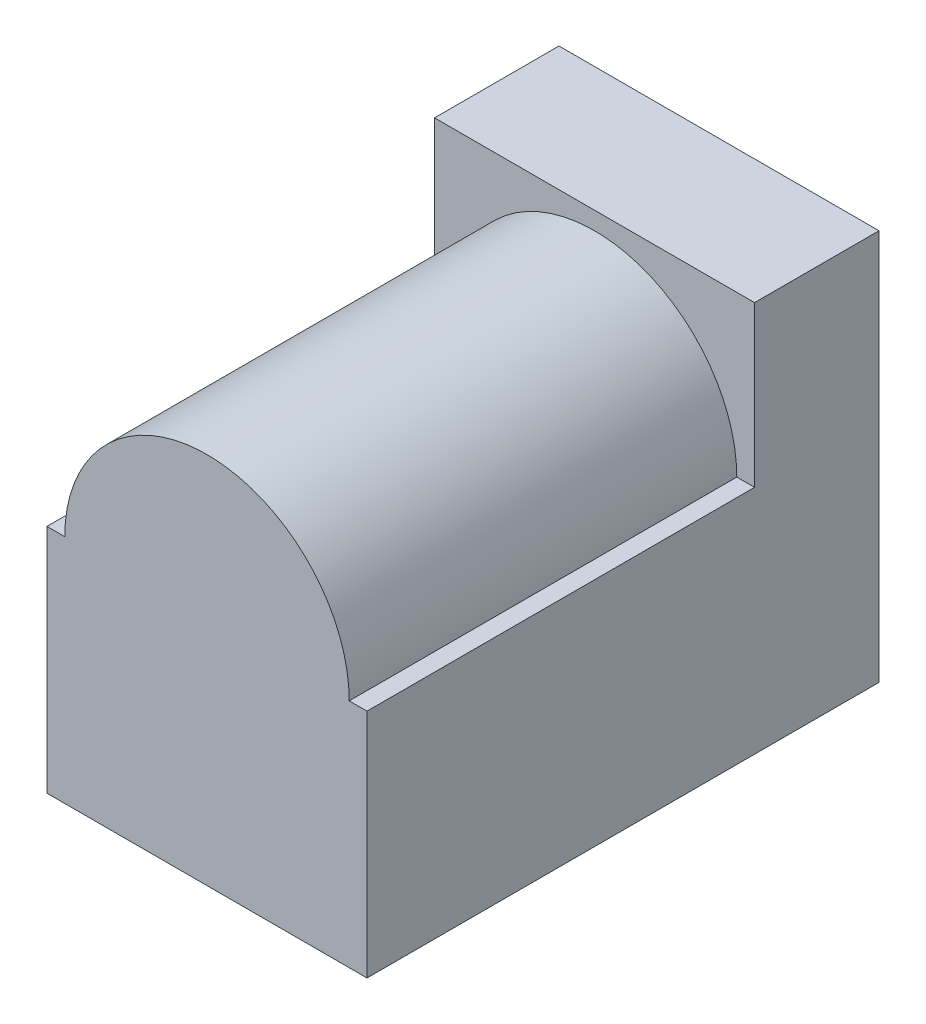
SolidWorks part; units mm, degrees
material "ABS PC"
ref_plane "Front Plane" through (0, 0, 0) normal (0, 0, 1) x (1, 0, 0)
ref_plane "Top Plane" through (0, 0, 0) normal (0, 1, 0) x (1, 0, 0)
ref_plane "Right Plane" through (0, 0, 0) normal (1, 0, 0) x (0, 0, -1)
sketch "Sketch1" plane through (0, 0, 0) normal (0, 0, 1) x (1, 0, 0)
  line L1 (0, 0) -> (9, 0)
  line L2 (0, 0) -> (0, 11)
  line L3 (0, 11) -> (9, 11)
  line L4 (9, 0) -> (9, 11)
  dimension "D1" = 9
  dimension "D2" = 11
extrude "Boss-Extrude1" add sketch "Sketch1" along normal blind 3.5
sketch "Sketch2" plane through (0, 0, 0) normal (0, 0, -1) x (-1, 0, 0)
  line L0 (0, 0) -> (-9, 0) construction
  line L1 (-0.5, 6.5) -> (0, 6.5)
  line L2 (0, 11) -> (0, 0) construction
  line L3 (0, 6.5) -> (0, 0)
  line L4 (0, 0) -> (-9, 0)
  line L5 (-9, 0) -> (-9, 6.5)
  line L6 (-9, 0) -> (-9, 11) construction
  line L7 (-9, 6.5) -> (-8.5, 6.5)
  arc A0 (-0.5, 6.5) -> (-8.5, 6.5) centre (-4.5, 6.5) ccw
  dimension "D1" = 8
  dimension "D2" = 4.5
  dimension "D3" = 6.5
extrude "Boss-Extrude2" add sketch "Sketch2" against normal blind 14.4
sketch "Sketch3" plane through (0, 0, 0) normal (0, 0, -1) x (-1, 0, 0)
  line L0 (0, 0) -> (-9, 0) construction
  line L2 (0, 11) -> (0, 0) construction
  circle A0 centre (-4.5, 6.5) radius 3.25
  circle A1 centre (-4.5, 6.5) radius 1
  dimension "D1" = 6.5
  dimension "D4" = 2
  dimension "D2" = 6.5
  dimension "D3" = 4.5
extrude "Cut-Extrude1" cut sketch "Sketch3" against normal blind 10
